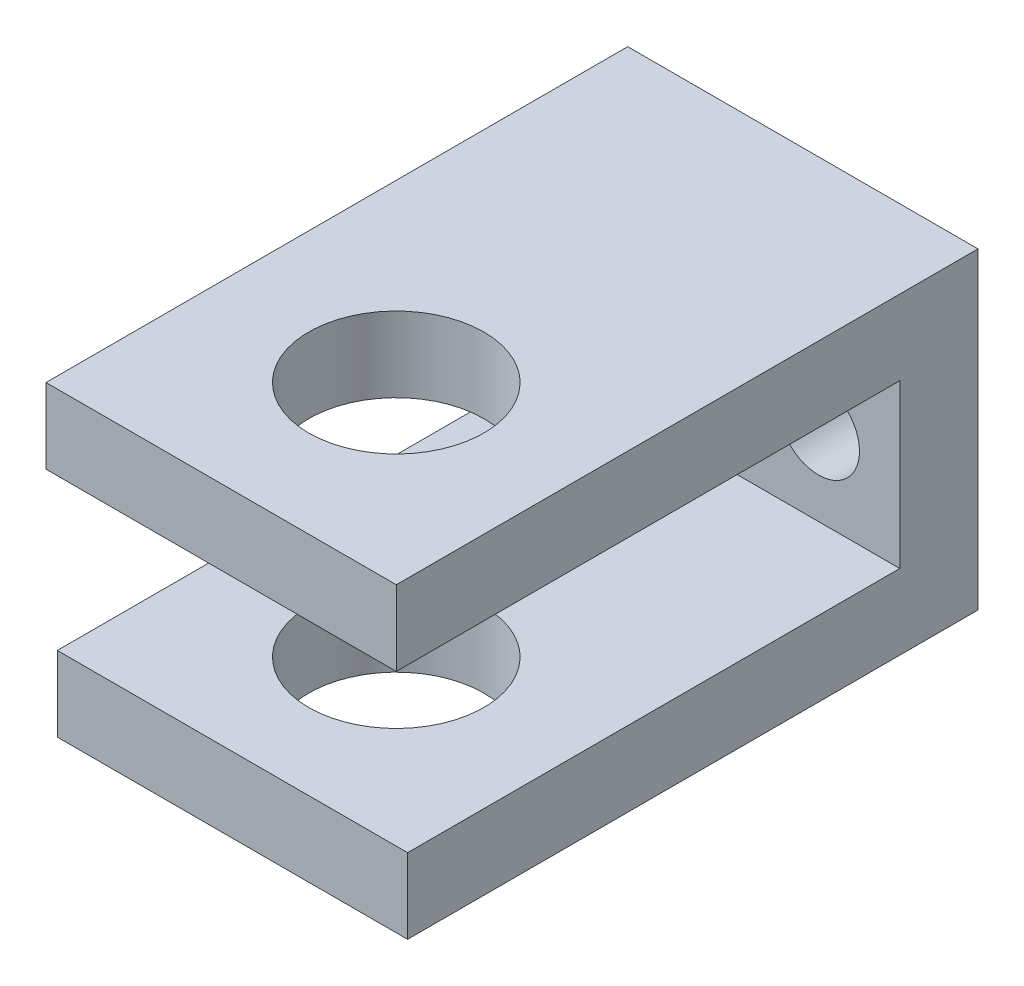
SolidWorks part; units mm, degrees
ref_plane "Front Plane" through (0, 0, 0) normal (0, 0, 1) x (1, 0, 0)
ref_plane "Top Plane" through (0, 0, 0) normal (0, 1, 0) x (1, 0, 0)
ref_plane "Right Plane" through (0, 0, 0) normal (1, 0, 0) x (0, 0, -1)
sketch "Sketch1" plane through (0, 0, 0) normal (0, 1, 0) x (1, 0, 0)
  line L1 (-7.112, -11.811) -> (7.112, -11.811)
  line L2 (-7.112, -11.811) -> (-7.112, 11.811)
  line L3 (-7.112, 11.811) -> (7.112, 11.811)
  line L4 (7.112, -11.811) -> (7.112, 11.811)
  line L5 (-7.112, -11.811) -> (7.112, 11.811) construction
  line L6 (-7.112, 11.811) -> (7.112, -11.811) construction
  point P0 (0, 0)
  dimension "D1" = 14.224
  dimension "D2" = 23.622
extrude "Boss-Extrude1" add sketch "Sketch1" along normal blind 3.048
sketch "Sketch2" plane through (7.112, 0, 0) normal (1, 0, 0) x (0, 0, -1)
  line L0 (11.811, 0) -> (8.636, 0)
  line L1 (11.811, 0) -> (11.811, -6.604)
  line L2 (8.636, 0) -> (8.636, -6.604)
  line L3 (11.811, -6.604) -> (8.636, -6.604)
  line L4 (-11.811, 0) -> (11.811, 0) construction
  dimension "D1" = 6.604
  dimension "D2" = 3.175
extrude "middle" add sketch "Sketch2" against normal blind 14.224
sketch "Sketch3" plane through (0, -6.604, 0) normal (0, -1, 0) x (1, 0, 0)
  line L0 (-7.112, -11.811) -> (7.112, -11.811)
  line L1 (-7.112, -11.811) -> (-7.112, 11.3517)
  line L2 (7.112, -11.811) -> (7.112, 11.3517)
  line L3 (-7.112, 11.3517) -> (7.112, 11.3517)
extrude "bottom" add sketch "Sketch3" along normal blind 3.048
sketch "Sketch4" plane through (0, 3.048, 0) normal (0, 1, 0) x (1, 0, 0)
  line L0 (7.112, 11.811) -> (-7.112, 11.811) construction
  line L4 (-7.112, -11.811) -> (7.112, -11.811) construction
  circle A0 centre (0, -4.699) radius 3.556
  dimension "D1" = 7.112
  dimension "D2" = 16.51
extrude "hole for clevis pin" cut sketch "Sketch4" against normal through all
sketch "Sketch5" plane through (0, 0, -11.811) normal (0, 0, -1) x (-1, 0, 0)
  line L0 (-7.112, -3.302) -> (7.112, -3.302) construction
  line L1 (-7.112, 3.048) -> (-7.112, -9.652) construction
  line L2 (7.112, 3.048) -> (7.112, -9.652) construction
  line L3 (0, 3.048) -> (0, -9.652) construction
  line L4 (-7.112, 3.048) -> (7.112, 3.048) construction
  line L5 (7.112, -9.652) -> (-7.112, -9.652) construction
  circle A0 centre (-3.81, -3.302) radius 1.6637
  circle A1 centre (3.81, -3.302) radius 1.6637
  dimension "D1" = 3.3274
  dimension "D2" = 3.81
  dimension "D3" = 3.3274
  dimension "D4" = 3.81
extrude "holes for screws" cut sketch "Sketch5" against normal through all
